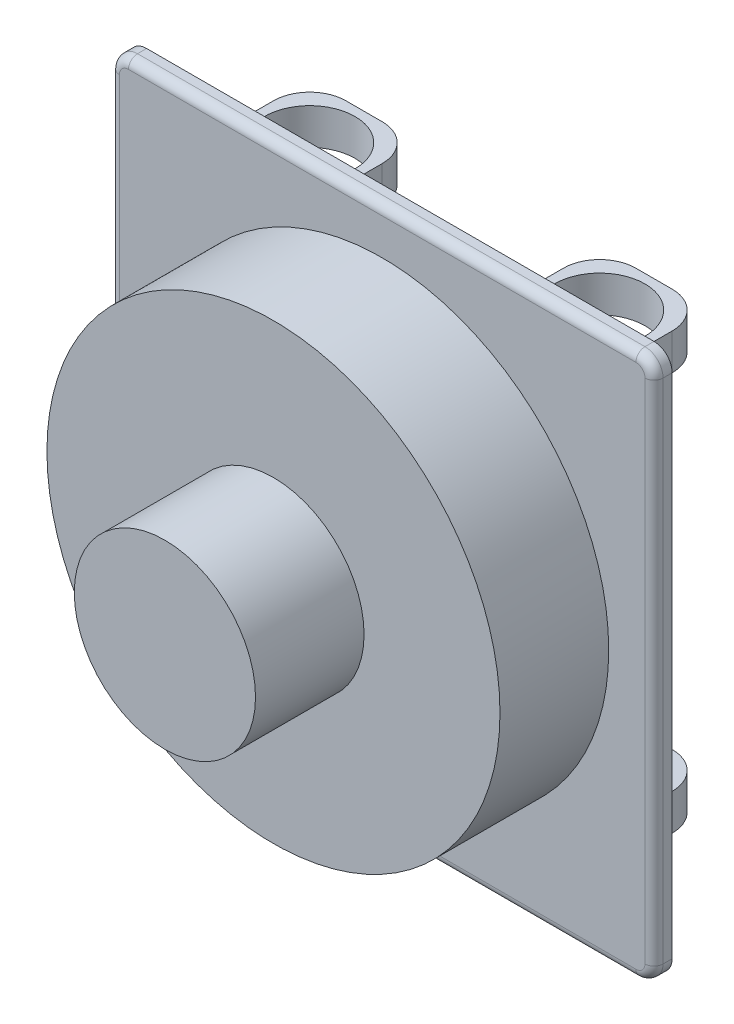
SolidWorks part; units mm, degrees
ref_plane "Front Plane" through (0, 0, 0) normal (0, 0, 1) x (1, 0, 0)
ref_plane "Top Plane" through (0, 0, 0) normal (0, 1, 0) x (1, 0, 0)
ref_plane "Right Plane" through (0, 0, 0) normal (1, 0, 0) x (0, 0, -1)
sketch "Sketch2" plane through (0, 0, 0) normal (0, 0, 1) x (1, 0, 0)
  line L1 (-140, 150) -> (140, 150)
  line L2 (-150, 140) -> (-150, -140)
  line L3 (-140, -150) -> (140, -150)
  line L4 (150, 140) -> (150, -140)
  line L5 (-150, 150) -> (150, -150) construction
  line L6 (-150, -150) -> (150, 150) construction
  arc A0 (-150, -140) -> (-140, -150) centre (-140, -140) ccw
  arc A1 (140, -150) -> (150, -140) centre (140, -140) ccw
  arc A2 (140, 150) -> (150, 140) centre (140, 140) cw
  arc A3 (-140, 150) -> (-150, 140) centre (-140, 140) ccw
  point P0 (0, 0)
  dimension "D2" = 10
  dimension "D1" = 300
extrude "Boss-Extrude1" add sketch "Sketch2" along normal blind 10
fillet "Fillet1" radius 5 8 edges at (147.0711, 147.0711, 10) (150, 0, 10) (147.0711, -147.0711, 10) (0, -150, 10) (-147.0711, -147.0711, 10) (-150, 0, 10) (-147.0711, 147.0711, 10) (0, 150, 10)
sketch "Sketch3" plane through (0, 0, 0) normal (0, 0, -1) x (-1, 0, 0)
  line L0 (0, 0) -> (0, 150) construction
  line L1 (-140, 150) -> (140, 150) construction
  line L3 (50, 120) -> (110, 120)
  line L4 (50, 120) -> (50, 100)
  line L5 (50, 100) -> (110, 100)
  line L6 (110, 120) -> (110, 100)
  line L7 (50, 120) -> (110, 100) construction
  line L8 (50, 100) -> (110, 120) construction
  line L9 (-110, 120) -> (-50, 120)
  line L10 (-110, 120) -> (-110, 100)
  line L11 (-110, 100) -> (-50, 100)
  line L12 (-50, 120) -> (-50, 100)
  line L13 (-110, 120) -> (-50, 100) construction
  line L14 (-110, 100) -> (-50, 120) construction
  line L15 (0, 0) -> (150, 0) construction
  line L16 (150, 140) -> (150, -140) construction
  line L17 (50, -100) -> (110, -120) construction
  line L18 (50, -120) -> (110, -100) construction
  line L19 (110, -120) -> (110, -100)
  line L20 (50, -100) -> (110, -100)
  line L21 (50, -120) -> (50, -100)
  line L22 (50, -120) -> (110, -120)
  line L23 (-110, -100) -> (-50, -120) construction
  line L24 (-110, -120) -> (-50, -100) construction
  line L25 (-50, -120) -> (-50, -100)
  line L26 (-110, -100) -> (-50, -100)
  line L27 (-110, -120) -> (-110, -100)
  line L28 (-110, -120) -> (-50, -120)
  point P5 (80, 110)
  point P10 (-80, 110)
  point P22 (80, -110)
  point P27 (-80, -110)
  dimension "D1" = 60
  dimension "D2" = 60
  dimension "D3" = 40
  dimension "D4" = 20
  dimension "D5" = 80
  dimension "D6" = 80
  dimension "D7" = 20
extrude "Boss-Extrude2" add sketch "Sketch3" along normal blind 60
fillet "Fillet2" radius 20 8 edges at (-110, 110, -60) (-50, 110, -60) (50, 110, -60) (110, 110, -60) (110, -110, -60) (50, -110, -60) (-110, -110, -60) (-50, -110, -60)
sketch "Sketch6" plane through (0, -120, 0) normal (0, -1, 0) x (1, 0, 0)
  line L0 (-70, -60) -> (-90, -60) construction
  line L1 (90, -60) -> (70, -60) construction
  circle A0 centre (-80, -30) radius 25
  circle A1 centre (80, -30) radius 25
  point P2 (-80, -60)
  point P7 (80, -60)
  point P11 (80, -30)
  point P12 (-80, -30)
  dimension "D1" = 50
  dimension "D2" = 30
  dimension "D3" = 30
extrude "Cut-Extrude1" cut sketch "Sketch6" against normal through all
sketch "Sketch7" plane through (0, 0, 10) normal (0, 0, 1) x (1, 0, 0)
  circle A0 centre (0, 0) radius 125
  dimension "D1" = 250
extrude "Boss-Extrude3" add sketch "Sketch7" along normal blind 60
sketch "Sketch8" plane through (0, 0, 70) normal (0, 0, 1) x (1, 0, 0)
  circle A0 centre (0, 0) radius 50
  dimension "D1" = 100
extrude "Boss-Extrude5" add sketch "Sketch8" along normal blind 59.9
